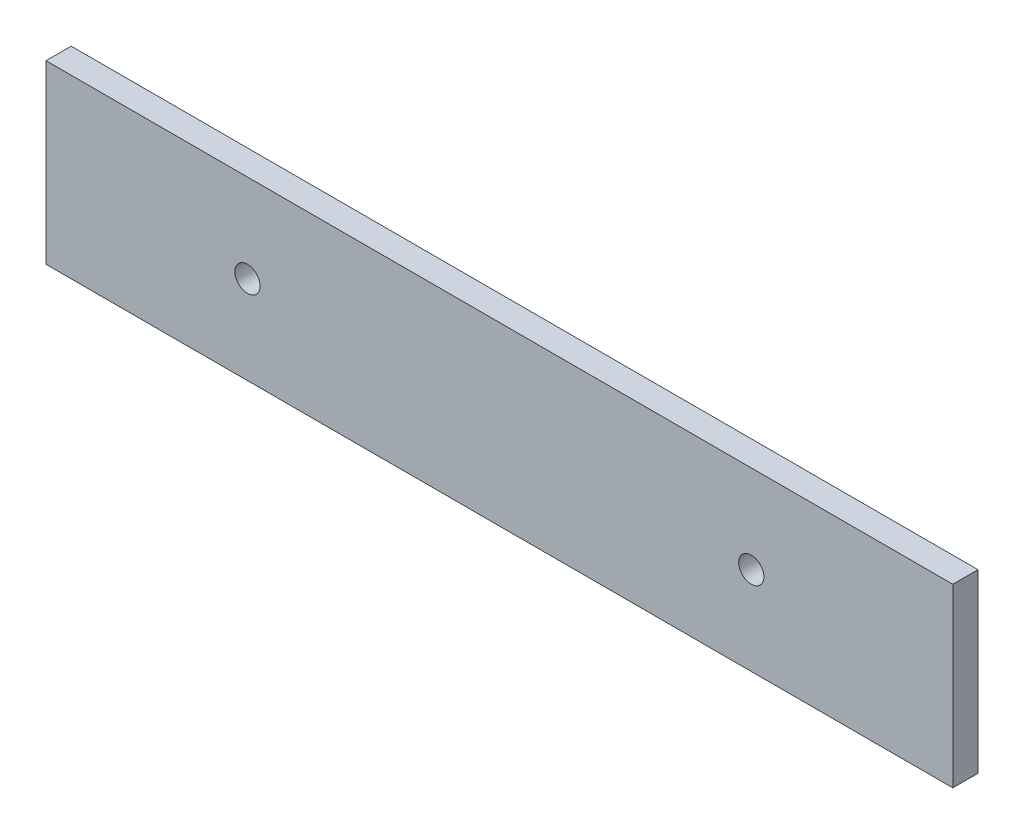
SolidWorks part; units mm, degrees
ref_plane "Plan de face" through (0, 0, 0) normal (0, 0, 1) x (1, 0, 0)
ref_plane "Plan de dessus" through (0, 0, 0) normal (0, 1, 0) x (1, 0, 0)
ref_plane "Plan de droite" through (0, 0, 0) normal (1, 0, 0) x (0, 0, -1)
sketch "Esquisse1" plane through (0, 0, 0) normal (0, 0, 1) x (1, 0, 0)
  line L1 (-147.0025, 155.6897) -> (-507.0025, 155.6897)
  line L2 (-147.0025, 155.6897) -> (-147.0025, 85.6897)
  line L3 (-147.0025, 85.6897) -> (-507.0025, 85.6897)
  line L4 (-507.0025, 155.6897) -> (-507.0025, 85.6897)
  circle A0 centre (-427.0025, 120.6897) radius 5
  circle A1 centre (-227.0025, 120.6897) radius 5
  dimension "D6" = 10
  dimension "D7" = 10
  dimension "D1" = 360
  dimension "D2" = 70
  dimension "D3" = 35
  dimension "D4" = 200
  dimension "D5" = 80
extrude "Boss.-Extru.1" add sketch "Esquisse1" along normal blind 10
